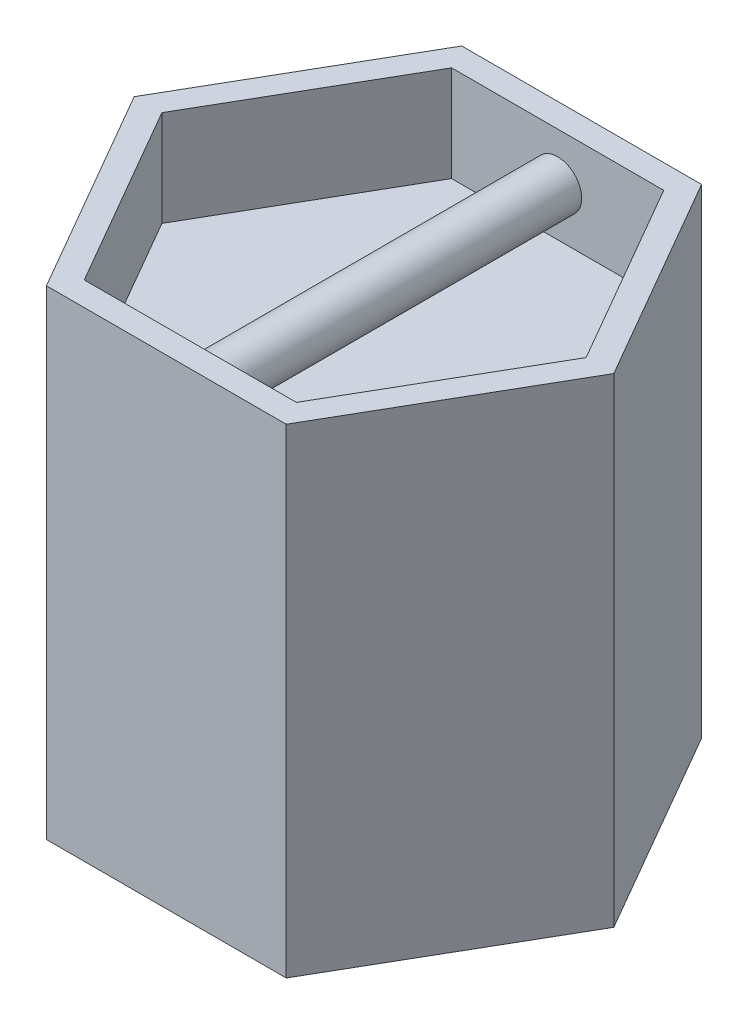
SolidWorks part; units mm, degrees
ref_plane "Front Plane" through (0, 0, 0) normal (0, 0, 1) x (1, 0, 0)
ref_plane "Top Plane" through (0, 0, 0) normal (0, 1, 0) x (1, 0, 0)
ref_plane "Right Plane" through (0, 0, 0) normal (1, 0, 0) x (0, 0, -1)
sketch "Sketch1" plane through (0, 0, 0) normal (0, 1, 0) x (1, 0, 0)
  line L1 (10, 0) -> (5, 8.6603)
  line L2 (5, 8.6603) -> (-5, 8.6603)
  line L3 (-5, 8.6603) -> (-10, 0)
  line L4 (-10, 0) -> (-5, -8.6603)
  line L5 (-5, -8.6603) -> (5, -8.6603)
  line L6 (5, -8.6603) -> (10, 0)
  circle A0 centre (0, 0) radius 8.6603 construction
  dimension "D1" = 10
extrude "Boss-Extrude1" add sketch "Sketch1" along normal blind 20
sketch "Sketch3" plane through (0, 20, 0) normal (0, 1, 0) x (1, 0, 0)
  line L22 (4.4226, -7.6603) -> (8.8453, 0)
  line L23 (8.8453, 0) -> (4.4226, 7.6603)
  line L24 (4.4226, 7.6603) -> (-4.4226, 7.6603)
  line L25 (-4.4226, 7.6603) -> (-8.8453, 0)
  line L26 (-8.8453, 0) -> (-4.4226, -7.6603)
  line L27 (-4.4226, -7.6603) -> (4.4226, -7.6603)
  line L28 (4.4226, -7.6603) -> (8.8453, 0)
  line L29 (8.8453, 0) -> (4.4226, 7.6603)
  line L30 (4.4226, 7.6603) -> (-4.4226, 7.6603)
  line L31 (-4.4226, 7.6603) -> (-8.8453, 0)
  line L32 (-8.8453, 0) -> (-4.4226, -7.6603)
  line L33 (-4.4226, -7.6603) -> (4.4226, -7.6603)
  dimension "D1" = 1
extrude "Cut-Extrude1" cut sketch "Sketch3" against normal blind 4
sketch "Sketch4" plane through (0, 0, 0) normal (0, 0, 1) x (1, 0, 0)
  circle A0 centre (0, 18) radius 1
  dimension "D1" = 2
  dimension "D2" = 18
extrude "Boss-Extrude2" add sketch "Sketch4" along normal up to next and the other way up to next
